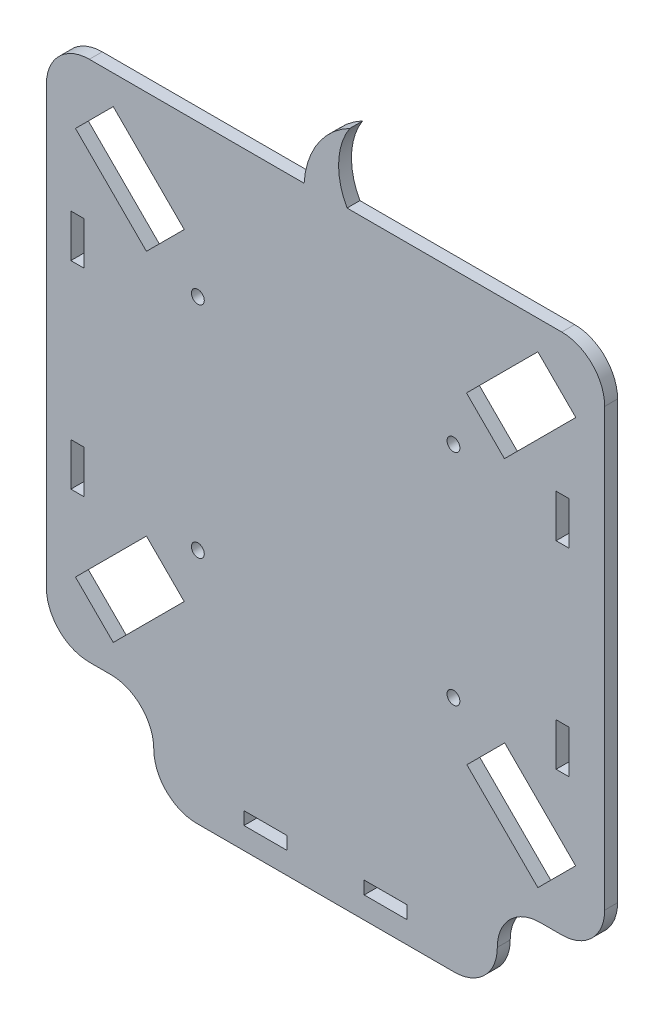
SolidWorks part; units mm, degrees
ref_plane "Alzado" through (0, 0, 0) normal (0, 0, 1) x (1, 0, 0)
ref_plane "Planta" through (0, 0, 0) normal (0, 1, 0) x (1, 0, 0)
ref_plane "Vista lateral" through (0, 0, 0) normal (1, 0, 0) x (0, 0, -1)
sketch "Model" plane through (0, 0, 0) normal (0, 0, 1) x (1, 0, 0)
  line L0 (53.7258, -62.4592) -> (53.7258, -59.4592)
  line L1 (53.7258, -59.4592) -> (63.7258, -59.4488)
  line L2 (63.7258, -59.4488) -> (63.7258, -62.4592)
  line L3 (63.7258, -62.4592) -> (53.7258, -62.4592)
  line L4 (25.7258, -62.4592) -> (25.7258, -59.4592)
  line L5 (25.7258, -59.4592) -> (35.7258, -59.4592)
  line L6 (35.7258, -59.4592) -> (35.7258, -62.4592)
  line L7 (35.7258, -62.4592) -> (25.7258, -62.4592)
  line L8 (-5.2742, -47.5263) -> (-10.2742, -47.5263)
  line L9 (-20.2742, -37.5263) -> (-20.2742, 64.0737)
  line L10 (-10.2742, 74.0737) -> (39.7291, 74.0737)
  line L11 (11.813, 50.7871) -> (3.0123, 41.9865)
  line L12 (-13.5114, 58.5102) -> (-4.7107, 67.3108)
  line L13 (3.0123, 41.9865) -> (-13.5114, 58.5102)
  line L14 (-4.7107, 67.3108) -> (11.813, 50.7871)
  line L15 (86.3907, 41.855) -> (103.0077, 58.472)
  line L16 (103.0077, 58.472) -> (94.1689, 67.3108)
  line L17 (77.5519, 50.6938) -> (86.3907, 41.855)
  line L18 (94.1689, 67.3108) -> (77.5519, 50.6938)
  line L19 (-13.5114, -31.9627) -> (-4.7107, -40.7634)
  line L20 (3.0123, -15.439) -> (-13.5114, -31.9627)
  line L21 (-4.7107, -40.7634) -> (11.813, -24.2397)
  line L22 (11.813, -24.2397) -> (3.0123, -15.439)
  line L23 (94.1689, -40.7634) -> (102.9696, -31.9628)
  line L24 (102.9696, -31.9628) -> (86.4459, -15.4391)
  line L25 (77.6452, -24.2397) -> (94.1689, -40.7634)
  line L26 (86.4459, -15.4391) -> (77.6452, -24.2397)
  line L27 (109.7325, 64.0737) -> (109.7325, -37.5263)
  line L28 (14.7258, -67.5322) -> (74.7258, -67.5322)
  line L29 (84.7258, -57.5322) -> (84.7258, -57.5263)
  line L30 (4.7258, -57.5322) -> (4.7258, -57.5263)
  line L31 (94.7258, -47.5263) -> (99.7325, -47.5263)
  line L32 (49.7291, 74.0737) -> (99.7325, 74.0737)
  line L33 (98.4136, 41.32) -> (101.4136, 41.32)
  line L34 (98.4136, -14.7725) -> (101.4136, -14.7725)
  line L35 (-14.5809, -14.7725) -> (-11.5809, -14.7725)
  line L36 (-14.5809, 41.32) -> (-11.5809, 41.32)
  line L37 (101.4136, -14.7725) -> (101.4136, -4.7725)
  line L38 (101.4136, 41.32) -> (101.4136, 31.32)
  line L39 (-11.5809, 41.32) -> (-11.5809, 31.32)
  line L40 (-11.5809, -14.7725) -> (-11.5809, -4.7725)
  line L41 (101.4136, 31.32) -> (98.4136, 31.32)
  line L42 (101.4136, -4.7725) -> (98.4136, -4.7725)
  line L43 (-11.5809, -4.7725) -> (-14.5809, -4.7725)
  line L44 (-11.5809, 31.32) -> (-14.5809, 31.32)
  line L45 (98.4136, 41.32) -> (98.4136, 31.32)
  line L46 (-14.5809, 41.32) -> (-14.5809, 31.32)
  line L47 (98.4136, -4.7725) -> (98.4136, -14.7725)
  line L48 (-14.5809, -4.7725) -> (-14.5809, -14.7725)
  circle A0 centre (74.5113, -12.2671) radius 1.5
  circle A1 centre (14.985, -12.3051) radius 1.5
  circle A2 centre (14.985, 38.8145) radius 1.5
  circle A3 centre (74.5113, 38.8145) radius 1.5
  arc A4 (99.7325, -47.5263) -> (109.7325, -37.5263) centre (99.7325, -37.5263) ccw
  arc A5 (109.7325, 64.0737) -> (99.7325, 74.0737) centre (99.7325, 64.0737) ccw
  arc A6 (-10.2742, 74.0737) -> (-20.2742, 64.0737) centre (-10.2742, 64.0737) ccw
  arc A7 (-20.2742, -37.5263) -> (-10.2742, -47.5263) centre (-10.2742, -37.5263) ccw
  arc A8 (4.7258, -57.5263) -> (-5.2742, -47.5263) centre (-5.2742, -57.5263) ccw
  arc A9 (4.7258, -57.5322) -> (14.7258, -67.5322) centre (14.7258, -57.5322) ccw
  arc A10 (74.7258, -67.5322) -> (84.7258, -57.5322) centre (74.7258, -57.5322) ccw
  arc A11 (94.7258, -47.5263) -> (84.7258, -57.5263) centre (94.7258, -57.5263) ccw
  arc A12 (50.735, 90.6524) -> (39.7291, 74.0737) centre (59.6401, 72.7982) ccw
  arc A13 (50.3742, 90.4678) -> (49.7291, 74.0737) centre (63.6537, 81.7356) ccw
extrude "Saliente-Extruir1" add sketch "Model" along normal blind 3 contours A13 A12 L10 A6 L9 A7 L8 A8 L30 A9 L28 A10 L29 A11 L31 A4 L27 A5 L32 A3 A2 A1 A0 L48 L43 L40 L35 L47 L42 L37 L34 L46 L36 L39 L44 L45 L33 L38 L41 L26 L24 L23
